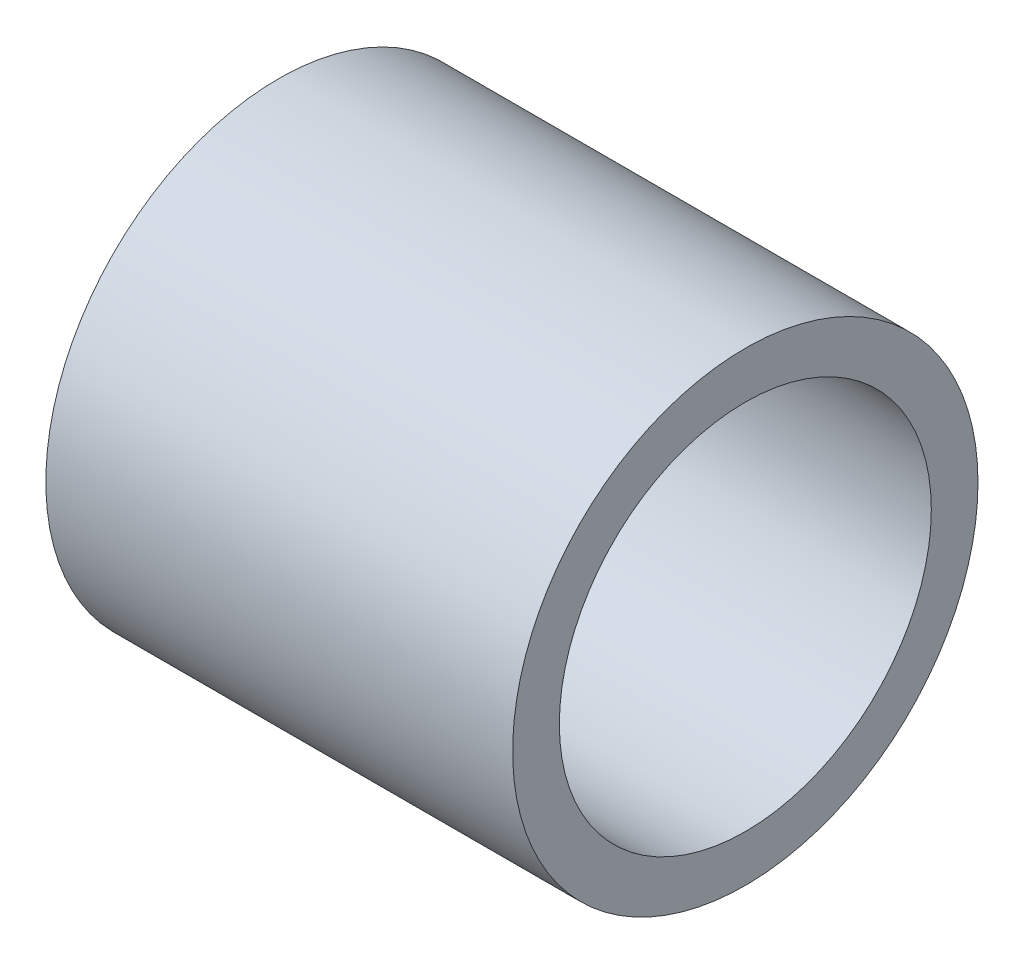
SolidWorks part; units mm, degrees
ref_plane "Front Plane" through (0, 0, 0) normal (0, 0, 1) x (1, 0, 0)
ref_plane "Top Plane" through (0, 0, 0) normal (0, 1, 0) x (1, 0, 0)
ref_plane "Right Plane" through (0, 0, 0) normal (1, 0, 0) x (0, 0, -1)
sketch "Sketch1" plane through (0, 0, 0) normal (1, 0, 0) x (0, 0, -1)
  circle A0 centre (0, 0) radius 15.825
  circle A1 centre (0, 0) radius 12.65
  dimension "D1" = 31.65
  dimension "D2" = 3.175
extrude "Boss-Extrude1" add sketch "Sketch1" along normal blind 31.75
